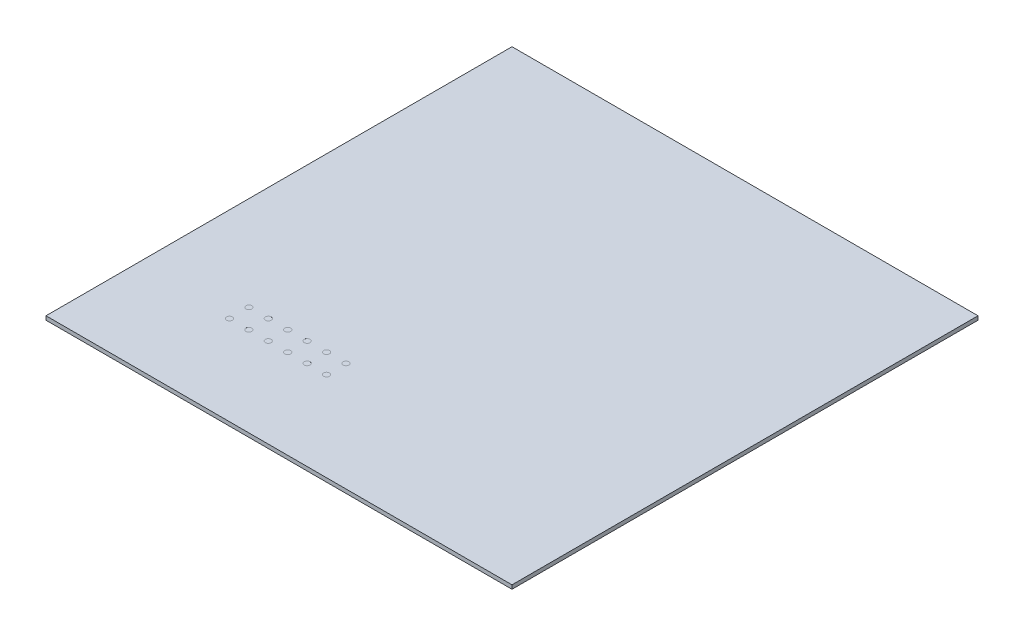
SolidWorks part; units mm, degrees
ref_plane "Front Plane" through (0, 0, 0) normal (0, 0, 1) x (1, 0, 0)
ref_plane "Top Plane" through (0, 0, 0) normal (0, 1, 0) x (1, 0, 0)
ref_plane "Right Plane" through (0, 0, 0) normal (1, 0, 0) x (0, 0, -1)
sketch "Sketch1" plane through (0, 0, 0) normal (0, 1, 0) x (1, 0, 0)
  line L1 (0, 0) -> (12000, 0)
  line L2 (0, 0) -> (0, 12000)
  line L3 (0, 12000) -> (12000, 12000)
  line L4 (12000, 0) -> (12000, 12000)
extrude "Boss-Extrude1" add sketch "Sketch1" along normal blind 100
sketch "Sketch5" plane through (0, 100, 0) normal (0, 1, 0) x (1, 0, 0)
  line L0 (0, 2550) -> (12000, 2550) construction
  line L1 (0, 12000) -> (0, 0) construction
  line L2 (12000, 0) -> (12000, 12000) construction
  line L3 (2425, 12000) -> (2425, 0) construction
  line L4 (12000, 12000) -> (0, 12000) construction
  line L5 (0, 0) -> (12000, 0) construction
  circle A0 centre (2425, 2800) radius 75
  circle A1 centre (2425, 2300) radius 75
  circle A2 centre (2925, 2300) radius 75
  circle A3 centre (3425, 2300) radius 75
  circle A4 centre (3925, 2300) radius 75
  circle A5 centre (4425, 2300) radius 75
  circle A6 centre (4925, 2300) radius 75
  circle A7 centre (2925, 2800) radius 75
  circle A8 centre (3425, 2800) radius 75
  circle A9 centre (3925, 2800) radius 75
  circle A10 centre (4425, 2800) radius 75
  circle A11 centre (4925, 2800) radius 75
  dimension "D3" = 150
  dimension "D4" = 250
  dimension "D7" = 2500
  dimension "D8" = 500
  dimension "D9" = 500
  dimension "D1" = 2425
  dimension "D2" = 2550
  dimension "D5" = 2
  dimension "D6" = 6
extrude "Cut-Extrude2" cut sketch "Sketch5" against normal blind 0.1
